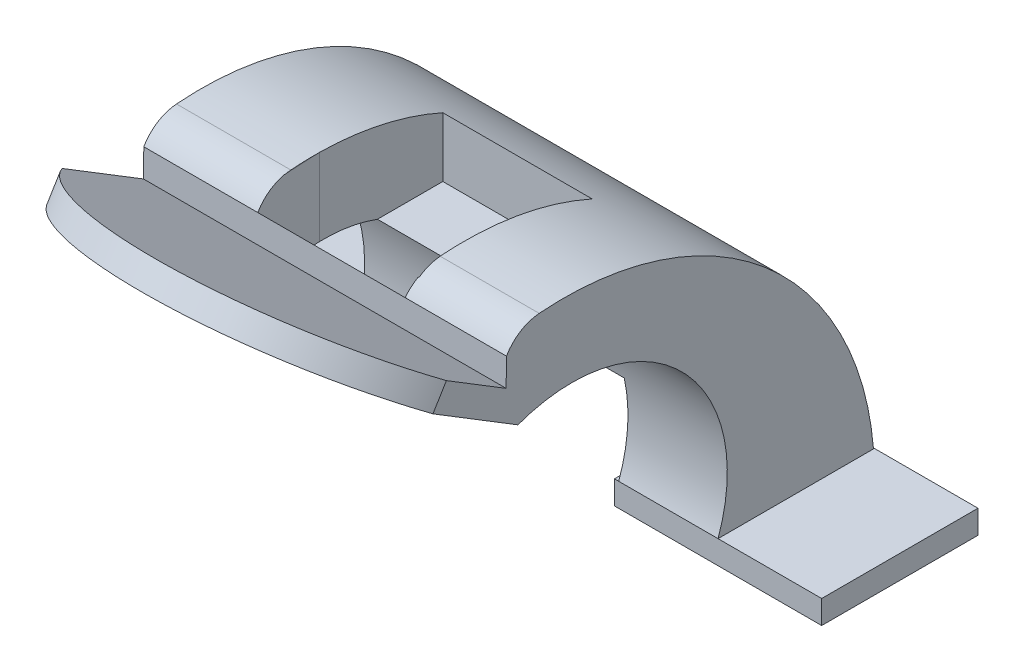
SolidWorks part; units mm, degrees
ref_plane "Front Plane" through (0, 0, 0) normal (0, 0, 1) x (1, 0, 0)
ref_plane "Top Plane" through (0, 0, 0) normal (0, 1, 0) x (1, 0, 0)
ref_plane "Right Plane" through (0, 0, 0) normal (1, 0, 0) x (0, 0, -1)
sketch "Sketch1" plane through (0, 0, 0) normal (1, 0, 0) x (0, 0, -1)
  line L0 (-9.2201, -23.7301) -> (-39.2201, -23.7301)
  line L1 (-77.8423, 14.5991) -> (-115.001, 37.3438)
  line L2 (-80.1197, 21.8435) -> (-111.5661, 41.0917)
  line L4 (-80.1197, 21.8435) -> (-80.0552, 27.1944)
  arc A0 (-9.2201, -23.7301) -> (-73.745, 31.1903) centre (-69.0202, -28.6234) ccw
  arc A1 (-39.2201, -23.7301) -> (-77.8423, 14.5991) centre (-67.4357, -13.5381) ccw
  arc A3 (-113.8991, 36.6693) -> (-111.5661, 41.0917) centre (-112.7326, 38.8805) cw
  arc A4 (-73.745, 31.1903) -> (-80.0552, 27.1944) centre (-73.1151, 23.2152) ccw
  dimension "D1" = 60
  dimension "D3" = 30
  dimension "D4" = 8
  dimension "D5" = 2.5
  dimension "D2" = 30
extrude "Boss-Extrude4" add sketch "Sketch1" against normal blind 70
sketch "Sketch7" plane through (0, -19.7849, 12.1102) normal (0, 0.8529, -0.5221) x (1, 0, 0)
  line L0 (0, -79.7383) -> (0, -93.2514)
  line L1 (0, -79.7383) -> (0, -116.608) construction
  line L2 (-70, -79.7383) -> (-70, -116.608) construction
  line L3 (-70, -98.1732) -> (-70, -79.7383)
  line L4 (-70, -79.7383) -> (0, -79.7383)
  line L5 (-70, -98.1732) -> (-70, -116.608)
  line L7 (-70, -116.608) -> (-70, -137.0873)
  line L8 (0, -116.608) -> (0, -93.2514)
  line L9 (-70, -137.0873) -> (0, -134.0197)
  line L10 (0, -134.0197) -> (0, -116.608)
  arc A0 (0, -93.2514) -> (-70, -98.1732) centre (-36.3396, -76.66) cw
  arc A1 (-36.3396, -116.608) -> (-70, -98.1732) centre (-36.3396, -76.66) cw
  arc A2 (0, -93.2514) -> (-36.3396, -116.608) centre (-36.3396, -76.66) cw
extrude "Cut-Extrude7" cut sketch "Sketch7" against normal blind 70 contours L9 L10 L7 M6 | A0 M3 M6 | A0 M6 M5
sketch3d "3DSketch2"
  line L0 (-70, -23.7301, 9.2201) -> (0, -23.7301, 9.2201) construction
  line L1 (-19.172, -23.7301, 9.2201) -> (-56.396, -23.7301, 9.2201)
  line L2 (-19.172, -23.7301, 9.2201) -> (-19.172, -6.9889, 9.2201)
  line L3 (-19.172, -6.9889, 9.2201) -> (-56.396, -6.9889, 9.2201)
  line L4 (-56.396, -23.7301, 9.2201) -> (-56.396, -6.9889, 9.2201)
extrude "Cut-Extrude8" cut sketch "3DSketch2" along direction (0, 0, 1) on the side of the normal blind 70 contours L2 L1 L4 L3
sketch3d "3DSketch3"
  line L0 (-70, 14.5991, 77.8423) -> (0, 14.5991, 77.8423) construction
  line L1 (-47.9276, 14.5991, 77.8423) -> (-47.9276, 14.5991, 44.4115)
  line L2 (-47.9276, 14.5991, 77.8423) -> (-19.1004, 14.5991, 77.8423)
  line L3 (-19.1004, 14.5991, 77.8423) -> (-19.1004, 14.5991, 44.4115)
  line L4 (-47.9276, 14.5991, 44.4115) -> (-19.1004, 14.5991, 44.4115)
extrude "Cut-Extrude9" cut sketch "3DSketch3" along direction (0, 1, 0) on the side against the normal blind 70
sketch3d "3DSketch4"
  line L0 (-70, 27.1944, 80.0552) -> (0, 27.1944, 80.0552) construction
  line L1 (-19.2265, 27.1944, 80.0552) -> (-19.1522, 27.7919, 68.2227)
  line L2 (-19.2265, 27.1944, 80.0552) -> (-48.0019, 30.7738, 80.0552)
  line L3 (-48.0019, 30.7738, 80.0552) -> (-47.9276, 31.3713, 68.2227)
  line L4 (-19.1522, 27.7919, 68.2227) -> (-47.9276, 31.3713, 68.2227)
  arc A0 (-47.9276, 26.0978, 44.4115) -> (-47.9276, 31.1903, 73.745) centre (-47.9276, -28.6234, 69.0202) ccw construction
  point P9 (12.0724, -28.6234, 69.0202)
extrude "Cut-Extrude10" cut sketch "3DSketch4" along direction (0, 1, 0) on the side against the normal blind 70
sketch "Sketch9" plane through (3.532, 28.3942, 1.4561) normal (-0.1233, -0.9911, -0.0508) x (-0.9924, 0.1231, 0.0063)
  line L0 (50.1054, -79.1331) -> (21.5495, -79.1331) construction
  line L1 (43.0021, -79.1331) -> (23.2596, -79.1331)
  line L2 (43.0021, -79.1331) -> (43.0021, -68.5061)
  line L3 (43.0021, -68.5061) -> (23.2596, -68.5061)
  line L4 (23.2596, -79.1331) -> (23.2596, -68.5061)
  ellipse E0 centre (15.8664, -70.3956) end of major axis (15.8664, -130.3956) minor radius 7.3968 (23.2604, -72.0508) -> (22.4483, -43.0166) ccw construction
  point P13 (44.5264, -76.6338)
extrude "Cut-Extrude11" cut sketch "Sketch9" against normal blind 70
sketch "Sketch10" plane through (0, 0, 0) normal (1, 0, 0) x (0, 0, -1)
  line L1 (-39.2201, -23.7301) -> (-9.0464, -23.7301)
  line L2 (-39.2201, -23.7301) -> (-39.2201, -28.2594)
  line L3 (-39.2201, -28.2594) -> (-9.0464, -28.2594)
  line L4 (-9.0464, -23.7301) -> (-9.0464, -28.2594)
extrude "Boss-Extrude6" add sketch "Sketch10" along normal blind 20 and the other way blind 20
sketch "Sketch11" plane through (-70, 0, 0) normal (-1, 0, 0) x (0, 0, 1)
  line L1 (9.0464, -23.7301) -> (39.2201, -23.7301)
  line L2 (9.0464, -23.7301) -> (9.0464, -28.2594)
  line L3 (9.0464, -28.2594) -> (39.2201, -28.2594)
  line L4 (39.2201, -23.7301) -> (39.2201, -28.2594)
extrude "Boss-Extrude7" add sketch "Sketch11" along normal blind 20 and the other way blind 20
sketch "Sketch12" plane through (0, 0, 9.0464) normal (0, 0, -1) x (-1, 0, 0)
  line L1 (44.4797, -23.3202) -> (56.8533, -23.3202)
  line L2 (44.4797, -23.3202) -> (44.4797, -30.7045)
  line L3 (44.4797, -30.7045) -> (56.8533, -30.7045)
  line L4 (56.8533, -23.3202) -> (56.8533, -30.7045)
extrude "Cut-Extrude12" cut sketch "Sketch12" against normal blind 60
